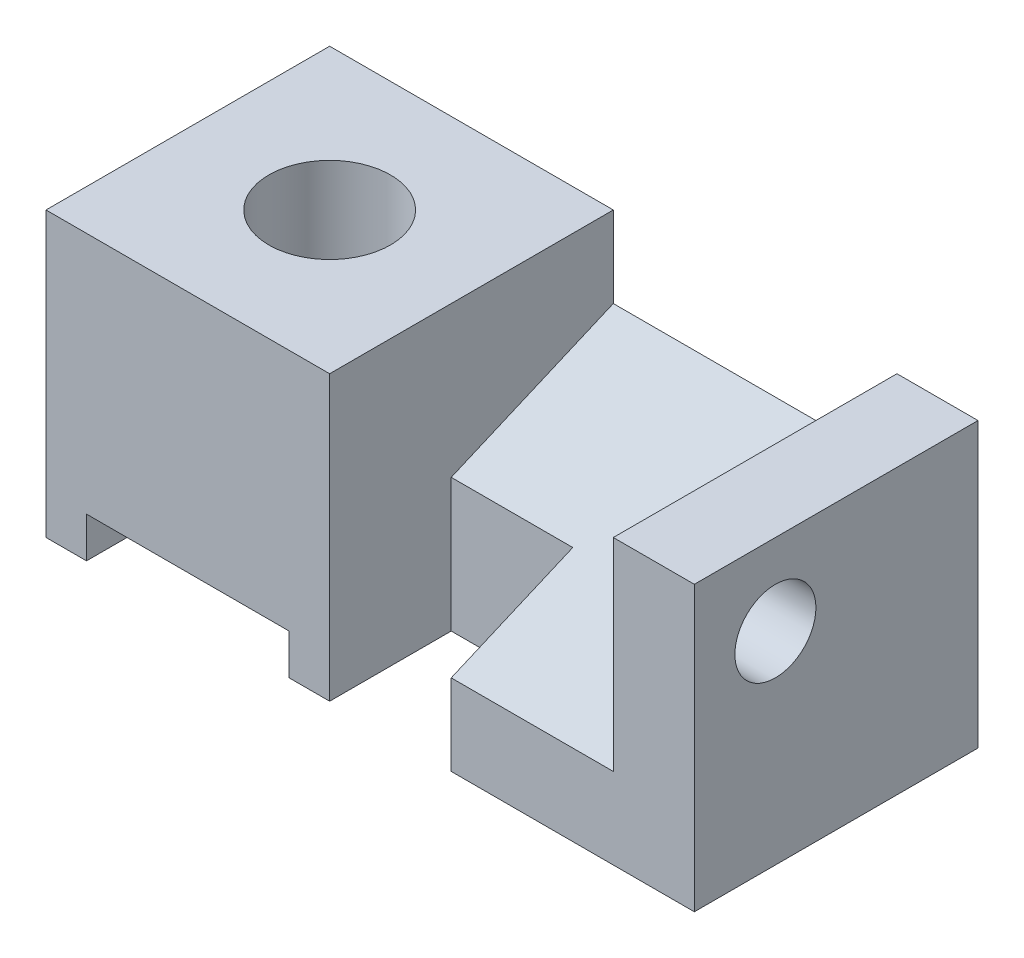
SolidWorks part; units mm, degrees
ref_plane "Front Plane" through (0, 0, 0) normal (0, 0, 1) x (1, 0, 0)
ref_plane "Top Plane" through (0, 0, 0) normal (0, 1, 0) x (1, 0, 0)
ref_plane "Right Plane" through (0, 0, 0) normal (1, 0, 0) x (0, 0, -1)
sketch "Sketch1" plane through (0, 0, 0) normal (0, 1, 0) x (1, 0, 0)
  line L1 (0, 0) -> (80, 0)
  line L2 (0, 0) -> (0, 35)
  line L3 (0, 35) -> (80, 35)
  line L4 (80, 0) -> (80, 35)
  dimension "D1" = 80
  dimension "D2" = 35
extrude "Boss-Extrude1" add sketch "Sketch1" along normal blind 35
sketch "Sketch2" plane through (80, 0, 0) normal (1, 0, 0) x (0, 0, -1)
  line L0 (35, 35) -> (35, 25)
  line L1 (35, 35) -> (35, 0) construction
  line L2 (35, 25) -> (0, 10)
  line L3 (0, 35) -> (0, 0) construction
  line L4 (0, 10) -> (0, 35)
  line L5 (0, 35) -> (35, 35)
  dimension "D1" = 25
  dimension "D2" = 10
extrude "Cut-Extrude1" cut sketch "Sketch2" against normal blind 45
sketch "Sketch3" plane through (80, 0, 0) normal (1, 0, 0) x (0, 0, -1)
  line L1 (35, 0) -> (0, 0)
  line L2 (35, 0) -> (35, 35)
  line L3 (35, 35) -> (0, 35)
  line L4 (0, 0) -> (0, 35)
  dimension "D1" = 35
extrude "Boss-Extrude2" add sketch "Sketch3" against normal blind 10
sketch "Sketch4" plane through (0, 0, 0) normal (0, -1, 0) x (-1, 0, 0)
  line L1 (-35, 0) -> (-50, 0)
  line L2 (-35, 0) -> (-35, 15)
  line L3 (-35, 15) -> (-50, 15)
  line L4 (-50, 0) -> (-50, 15)
  dimension "D1" = 15
  dimension "D2" = 15
extrude "Cut-Extrude2" cut sketch "Sketch4" against normal through all both and the other way through all
sketch "Sketch5" plane through (80, 0, 0) normal (1, 0, 0) x (0, 0, -1)
  line L0 (0, 35) -> (10, 35) construction
  line L1 (35, 35) -> (0, 35) construction
  line L2 (10, 35) -> (10, 25) construction
  circle A0 centre (10, 25) radius 5
  dimension "D1" = 10
  dimension "D2" = 10
extrude "Cut-Extrude3" cut sketch "Sketch5" against normal blind 10
sketch "Sketch6" plane through (0, 0, 0) normal (0, 0, 1) x (1, 0, 0)
  line L0 (0, 0) -> (5, 0) construction
  line L1 (0, 0) -> (35, 0) construction
  line L3 (5, 0) -> (30, 0)
  line L4 (5, 0) -> (5, 5)
  line L5 (5, 5) -> (30, 5)
  line L6 (30, 0) -> (30, 5)
  dimension "D1" = 5
  dimension "D2" = 25
  dimension "D3" = 5
extrude "Cut-Extrude4" cut sketch "Sketch6" against normal through all
sketch "Sketch7" plane through (0, 35, 0) normal (0, 1, 0) x (1, 0, 0)
  line L0 (0, 35) -> (17.5, 35) construction
  line L1 (35, 35) -> (0, 35) construction
  line L2 (17.5, 35) -> (17.5, 17.5) construction
  circle A0 centre (17.5, 17.5) radius 7.5
extrude "Cut-Extrude5" cut sketch "Sketch7" against normal through all contours A0
